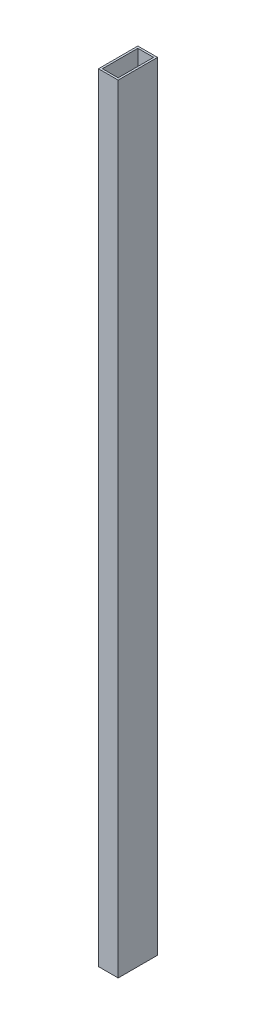
SolidWorks part; units mm, degrees
ref_plane "Спереди" through (0, 0, 0) normal (0, 0, 1) x (1, 0, 0)
ref_plane "Сверху" through (0, 0, 0) normal (0, 1, 0) x (1, 0, 0)
ref_plane "Справа" through (0, 0, 0) normal (1, 0, 0) x (0, 0, -1)
sketch "Эскиз1" plane through (0, 0, 0) normal (0, 1, 0) x (1, 0, 0)
  line L1 (-10, 20) -> (10, 20)
  line L2 (-10, 20) -> (-10, -20)
  line L3 (-10, -20) -> (10, -20)
  line L4 (10, 20) -> (10, -20)
  line L5 (-10, 20) -> (10, -20) construction
  line L6 (-10, -20) -> (10, 20) construction
  point P0 (0, 0)
extrude "Вытянуть-Тонкостенный1" add sketch "Эскиз1" along normal blind 790 thin
